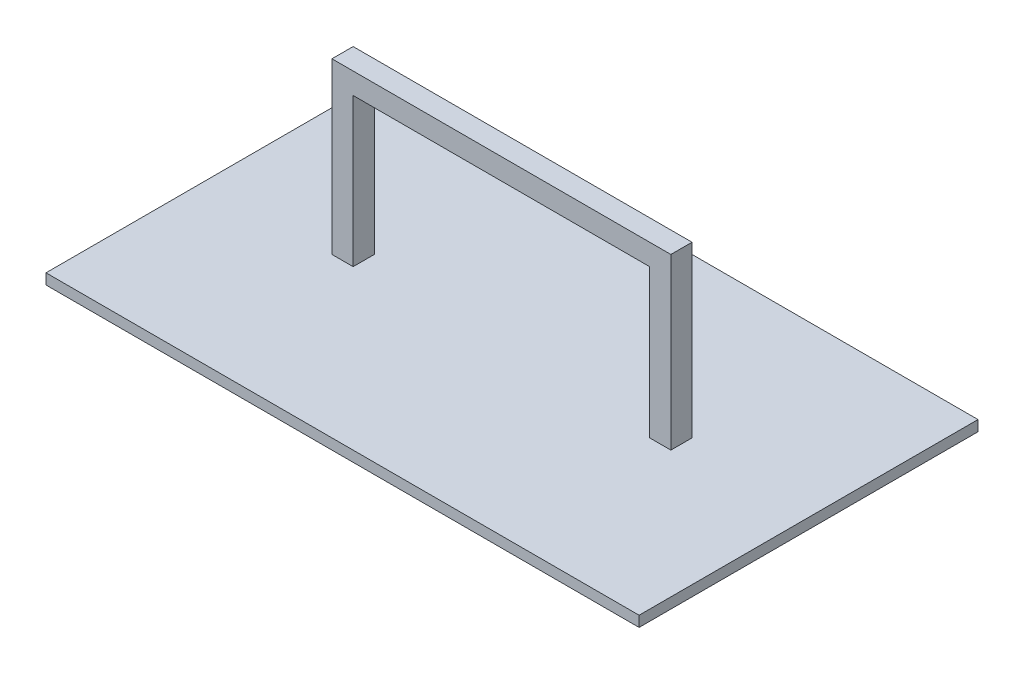
SolidWorks part; units mm, degrees
ref_plane "Front Plane" through (0, 0, 0) normal (0, 0, 1) x (1, 0, 0)
ref_plane "Top Plane" through (0, 0, 0) normal (0, 1, 0) x (1, 0, 0)
ref_plane "Right Plane" through (0, 0, 0) normal (1, 0, 0) x (0, 0, -1)
sketch "Sketch1" plane through (0, 0, 0) normal (0, 1, 0) x (1, 0, 0)
  line L0 (0, 101.6) -> (0, -101.6) construction
  line L1 (-177.8, 101.6) -> (177.8, 101.6)
  line L2 (-177.8, 101.6) -> (-177.8, -101.6)
  line L3 (-177.8, -101.6) -> (177.8, -101.6)
  line L4 (177.8, 101.6) -> (177.8, -101.6)
  point P6 (0, 0)
  dimension "D1" = 355.6
  dimension "D2" = 203.2
extrude "Boss-Extrude1" add sketch "Sketch1" along normal mid plane 6.35
sketch "Sketch2" plane through (0, 0, 0) normal (0, 0, 1) x (1, 0, 0)
  line L0 (-101.6, 3.175) -> (-101.6, 104.775)
  line L1 (-177.8, 3.175) -> (177.8, 3.175) construction
  line L2 (-101.6, 104.775) -> (101.6, 104.775)
  line L3 (101.6, 104.775) -> (101.6, 3.175)
  line L4 (101.6, 3.175) -> (88.9, 3.175)
  line L5 (88.9, 3.175) -> (88.9, 92.075)
  line L6 (88.9, 92.075) -> (-88.9, 92.075)
  line L7 (-88.9, 92.075) -> (-88.9, 3.175)
  line L8 (-88.9, 3.175) -> (-101.6, 3.175)
  line L9 (0, 92.075) -> (0, 0) construction
  dimension "D1" = 12.7
  dimension "D2" = 12.7
  dimension "D3" = 203.2
  dimension "D4" = 101.6
extrude "Boss-Extrude2" add sketch "Sketch2" along normal mid plane 12.7
